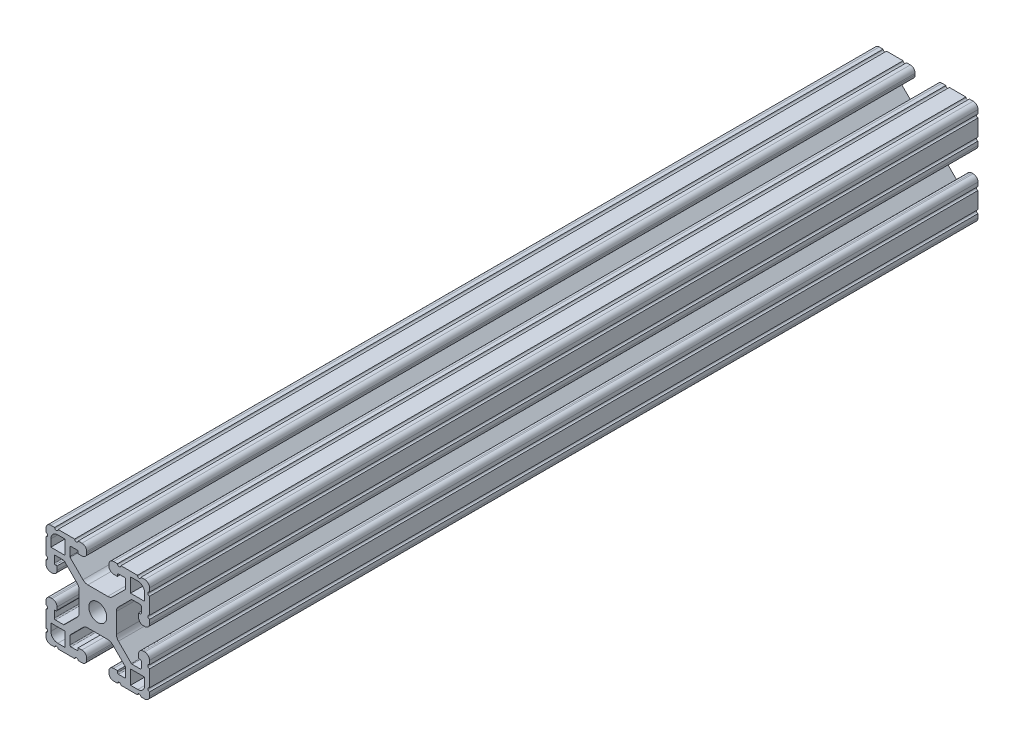
SolidWorks part; units mm, degrees
material "1023 Carbon Steel Sheet (SS)"
ref_plane "Front Plane" through (0, 0, 0) normal (0, 0, 1) x (1, 0, 0)
ref_plane "Top Plane" through (0, 0, 0) normal (0, 1, 0) x (1, 0, 0)
ref_plane "Right Plane" through (0, 0, 0) normal (1, 0, 0) x (0, 0, -1)
sketch "Sketch1" plane through (0, 0, 0) normal (0, 0, 1) x (1, 0, 0)
  line L0 (0, -19.05) -> (0, 19.05) construction
  line L1 (19.05, 0) -> (-19.05, 0) construction
  line L2 (4.064, 19.05) -> (-4.064, 19.05) construction
  line L3 (0, -6.858) -> (0, 6.858) construction
  line L4 (-4.064, 19.05) -> (-4.064, 14.986) construction
  line L5 (19.05, -10.287) -> (19.05, 10.287) construction
  line L6 (0, -3.302) -> (0, 3.302) construction
  point P4 (0, 0)
  point P8 (0, 0)
  point P11 (0, 19.05)
  point P14 (0, 0)
  point P18 (19.05, 0)
  point P21 (0, 0)
  dimension "Rail Width" = 38.1
  dimension "Rail Height" = 38.1
  dimension "T-Slot Width" = 8.128
  dimension "Thickness" = 4.064
  dimension "Opening Width" = 20.574
  dimension "Center Hole Diameter" = 6.604
  dimension "Slot Depth" = 12.192
sketch "Sketch2" plane through (0, 0, 0) normal (1, 0, 0) x (0, 0, -1)
  line L0 (-152.4, 0) -> (152.4, 0) construction
  line L1 (0, 19.05) -> (0, -19.05) construction
  line L2 (-25.4, 19.05) -> (25.4, 19.05) construction
  line L4 (3048, -19.05) -> (-3048, -19.05) construction
  point P0 (101.6, 0)
  point P3 (-101.6, 0)
  point P4 (0, 0)
  dimension "D1" = 50.8
  dimension "Rep Length" = 304.8
  dimension "D2" = 50.8
  dimension "Length Range [Min]" = 50.8
  dimension "Length Range [Max]" = 6096
sketch "Sketch3" plane through (0, 0, 0) normal (0, 0, 1) x (1, 0, 0)
  line L1 (19.05, -19.05) -> (-19.05, -19.05)
  line L2 (19.05, -19.05) -> (19.05, 19.05)
  line L3 (19.05, 19.05) -> (-19.05, 19.05)
  line L4 (-19.05, -19.05) -> (-19.05, 19.05)
  line L5 (19.05, -19.05) -> (-19.05, 19.05) construction
  line L6 (19.05, 19.05) -> (-19.05, -19.05) construction
  point P0 (0, 0)
extrude "Boss-Extrude1" add sketch "Sketch3" along normal up to vertex (152.4 mm away) and the other way up to vertex (152.4 mm away) up to point (0, 0, 152.4) other way up to point (0, 0, -152.4)
sketch "Sketch4" plane through (0, 0, 152.4) normal (0, 0, 1) x (1, 0, 0)
  line L4 (4.064, 14.986) -> (4.064, 19.05)
  line L5 (7.239, 14.986) -> (4.064, 14.986)
  line L6 (19.05, 0) -> (-19.05, 0) construction
  line L7 (4.7027, 6.858) -> (-4.7027, 6.858)
  line L8 (-4.7027, 6.858) -> (-10.287, 12.4423)
  line L37 (-19.05, 19.05) -> (-19.05, -19.05) construction
  line L38 (-19.05, -19.05) -> (19.05, -19.05) construction
  line L39 (-10.287, 12.4423) -> (-10.287, 16.002)
  line L40 (-10.287, 16.002) -> (-7.239, 16.002)
  line L41 (-7.239, 16.002) -> (-7.239, 14.986)
  line L42 (-7.239, 14.986) -> (-4.064, 14.986)
  line L43 (-4.064, 14.986) -> (-4.064, 19.05)
  line L44 (-4.064, 19.05) -> (4.064, 19.05)
  line L45 (0, 19.05) -> (0, 0) construction
  line L46 (-19.05, 19.05) -> (0, 0) construction
  line L47 (7.239, 16.002) -> (7.239, 14.986)
  line L48 (10.287, 16.002) -> (7.239, 16.002)
  line L49 (10.287, 12.4423) -> (10.287, 16.002)
  line L50 (4.7027, 6.858) -> (10.287, 12.4423)
  line L51 (-19.05, 0) -> (19.05, 0) construction
  line L52 (4.7027, -6.858) -> (10.287, -12.4423)
  line L53 (10.287, -12.4423) -> (10.287, -16.002)
  line L54 (10.287, -16.002) -> (7.239, -16.002)
  line L55 (7.239, -16.002) -> (7.239, -14.986)
  line L56 (-4.064, -19.05) -> (4.064, -19.05)
  line L57 (-4.064, -14.986) -> (-4.064, -19.05)
  line L58 (-7.239, -14.986) -> (-4.064, -14.986)
  line L59 (-7.239, -16.002) -> (-7.239, -14.986)
  line L60 (-10.287, -16.002) -> (-7.239, -16.002)
  line L61 (-10.287, -12.4423) -> (-10.287, -16.002)
  line L62 (-4.7027, -6.858) -> (-10.287, -12.4423)
  line L63 (4.7027, -6.858) -> (-4.7027, -6.858)
  line L64 (7.239, -14.986) -> (4.064, -14.986)
  line L65 (4.064, -14.986) -> (4.064, -19.05)
  line L66 (-6.858, -4.7027) -> (-12.4423, -10.287)
  line L67 (-12.4423, -10.287) -> (-16.002, -10.287)
  line L68 (-16.002, -10.287) -> (-16.002, -7.239)
  line L69 (-16.002, -7.239) -> (-14.986, -7.239)
  line L70 (-19.05, 4.064) -> (-19.05, -4.064)
  line L71 (-14.986, 4.064) -> (-19.05, 4.064)
  line L72 (-14.986, 7.239) -> (-14.986, 4.064)
  line L73 (-16.002, 7.239) -> (-14.986, 7.239)
  line L74 (-16.002, 10.287) -> (-16.002, 7.239)
  line L75 (-12.4423, 10.287) -> (-16.002, 10.287)
  line L76 (-6.858, 4.7027) -> (-12.4423, 10.287)
  line L77 (-6.858, -4.7027) -> (-6.858, 4.7027)
  line L78 (-14.986, -7.239) -> (-14.986, -4.064)
  line L79 (-14.986, -4.064) -> (-19.05, -4.064)
  line L80 (14.986, -4.064) -> (19.05, -4.064)
  line L81 (14.986, -7.239) -> (14.986, -4.064)
  line L82 (6.858, -4.7027) -> (6.858, 4.7027)
  line L83 (6.858, 4.7027) -> (12.4423, 10.287)
  line L84 (12.4423, 10.287) -> (16.002, 10.287)
  line L85 (16.002, 10.287) -> (16.002, 7.239)
  line L86 (16.002, 7.239) -> (14.986, 7.239)
  line L87 (14.986, 7.239) -> (14.986, 4.064)
  line L88 (14.986, 4.064) -> (19.05, 4.064)
  line L89 (19.05, 4.064) -> (19.05, -4.064)
  line L90 (16.002, -7.239) -> (14.986, -7.239)
  line L91 (16.002, -10.287) -> (16.002, -7.239)
  line L92 (12.4423, -10.287) -> (16.002, -10.287)
  line L93 (6.858, -4.7027) -> (12.4423, -10.287)
  line L94 (19.05, -19.05) -> (19.05, 19.05) construction
  line L95 (12.065, 17.272) -> (17.272, 17.272)
  line L96 (12.065, 17.272) -> (12.065, 12.065)
  line L97 (12.065, 12.065) -> (17.272, 12.065)
  line L98 (17.272, 17.272) -> (17.272, 12.065)
  line L99 (19.05, 19.05) -> (-19.05, 19.05) construction
  line L100 (17.272, -17.272) -> (17.272, -12.065)
  line L101 (12.065, -17.272) -> (17.272, -17.272)
  line L102 (12.065, -17.272) -> (12.065, -12.065)
  line L103 (12.065, -12.065) -> (17.272, -12.065)
  line L104 (-17.272, 17.272) -> (-17.272, 12.065)
  line L105 (-12.065, 12.065) -> (-17.272, 12.065)
  line L106 (-12.065, 17.272) -> (-12.065, 12.065)
  line L107 (-12.065, 17.272) -> (-17.272, 17.272)
  line L108 (-12.065, -12.065) -> (-17.272, -12.065)
  line L109 (-12.065, -17.272) -> (-12.065, -12.065)
  line L110 (-12.065, -17.272) -> (-17.272, -17.272)
  line L111 (-17.272, -17.272) -> (-17.272, -12.065)
  circle A5 centre (0, 0) radius 3.302
  point P21 (0, 6.858)
  point P23 (0, -6.858)
  point P38 (-6.858, 0)
  point P53 (6.858, 0)
  dimension "D1" = 20.574
  dimension "D2" = 3.048
  dimension "D3" = 3.048
  dimension "D4" = 3.048
  dimension "D5" = 1.778
  dimension "D6" = 1.778
  dimension "D7" = 1.778
extrude "Cut-Extrude1" cut sketch "Sketch4" against normal through all
sketch "Sketch5" plane through (0, 0, 152.4) normal (0, 0, 1) x (1, 0, 0)
  line L4 (-4.064, 19.05) -> (-19.05, 19.05) construction
  line L26 (-19.05, 19.05) -> (-19.05, 4.064) construction
  line L27 (-15.875, 19.05) -> (-14.605, 19.05)
  line L28 (-8.509, 19.05) -> (-7.239, 19.05)
  line L29 (-19.05, 15.875) -> (-19.05, 14.605)
  line L30 (-19.05, 8.509) -> (-19.05, 7.239)
  line L31 (8.509, 19.05) -> (7.239, 19.05)
  line L32 (15.875, 19.05) -> (14.605, 19.05)
  line L33 (19.05, 15.875) -> (19.05, 14.605)
  line L34 (19.05, 8.509) -> (19.05, 7.239)
  line L35 (19.05, -8.509) -> (19.05, -7.239)
  line L36 (19.05, -15.875) -> (19.05, -14.605)
  line L37 (15.875, -19.05) -> (14.605, -19.05)
  line L38 (8.509, -19.05) -> (7.239, -19.05)
  line L39 (-8.509, -19.05) -> (-7.239, -19.05)
  line L40 (-15.875, -19.05) -> (-14.605, -19.05)
  line L41 (-19.05, -15.875) -> (-19.05, -14.605)
  line L42 (-19.05, -8.509) -> (-19.05, -7.239)
  line L43 (19.05, 19.05) -> (4.064, 19.05) construction
  line L44 (19.05, 4.064) -> (19.05, 19.05) construction
  line L48 (-14.986, 4.064) -> (-19.05, 4.064) construction
  line L49 (-4.064, 14.986) -> (-4.064, 19.05) construction
  arc A8 (-15.875, 19.05) -> (-14.605, 19.05) centre (-15.24, 19.05) ccw
  arc A9 (-8.509, 19.05) -> (-7.239, 19.05) centre (-7.874, 19.05) ccw
  arc A10 (-19.05, 14.605) -> (-19.05, 15.875) centre (-19.05, 15.24) ccw
  arc A11 (-19.05, 7.239) -> (-19.05, 8.509) centre (-19.05, 7.874) ccw
  arc A12 (7.239, 19.05) -> (8.509, 19.05) centre (7.874, 19.05) ccw
  arc A13 (14.605, 19.05) -> (15.875, 19.05) centre (15.24, 19.05) ccw
  arc A14 (19.05, 15.875) -> (19.05, 14.605) centre (19.05, 15.24) ccw
  arc A15 (19.05, 8.509) -> (19.05, 7.239) centre (19.05, 7.874) ccw
  arc A16 (19.05, -7.239) -> (19.05, -8.509) centre (19.05, -7.874) ccw
  arc A17 (19.05, -14.605) -> (19.05, -15.875) centre (19.05, -15.24) ccw
  arc A18 (15.875, -19.05) -> (14.605, -19.05) centre (15.24, -19.05) ccw
  arc A19 (8.509, -19.05) -> (7.239, -19.05) centre (7.874, -19.05) ccw
  arc A20 (-7.239, -19.05) -> (-8.509, -19.05) centre (-7.874, -19.05) ccw
  arc A21 (-14.605, -19.05) -> (-15.875, -19.05) centre (-15.24, -19.05) ccw
  arc A22 (-19.05, -15.875) -> (-19.05, -14.605) centre (-19.05, -15.24) ccw
  arc A23 (-19.05, -8.509) -> (-19.05, -7.239) centre (-19.05, -7.874) ccw
  dimension "D2" = 0.635
  dimension "D4" = 3.81
  dimension "D5" = 3.81
  dimension "D1" = 3.81
  dimension "D3" = 3.81
  dimension "D7" = 4
extrude "Cut-Extrude2" cut sketch "Sketch5" against normal through all
fillet "Fillet1" radius 2.54 12 edges at (-6.858, 4.7027, 0) (-6.858, -4.7027, 0) (4.7027, -6.858, 0) (-4.7027, -6.858, 0) (6.858, -4.7027, 0) (6.858, 4.7027, 0) (4.7027, 6.858, 0) (-4.7027, 6.858, 0) (-17.272, 17.272, 0) (17.272, 17.272, 0) (17.272, -17.272, 0) (-17.272, -17.272, 0)
fillet "Fillet2" radius 1.778 20 edges at (19.05, -19.05, 0) (19.05, 19.05, 0) (-19.05, -19.05, 0) (-19.05, 19.05, 0) (-14.986, 4.064, 0) (-19.05, 4.064, 0) (-19.05, -4.064, 0) (-14.986, -4.064, 0) (-4.064, -19.05, 0) (-4.064, -14.986, 0) (4.064, -14.986, 0) (4.064, -19.05, 0) (19.05, -4.064, 0) (14.986, -4.064, 0) (19.05, 4.064, 0) (14.986, 4.064, 0) (4.064, 14.986, 0) (4.064, 19.05, 0) (-4.064, 19.05, 0) (-4.064, 14.986, 0)
fillet "Fillet3" radius 0.3969 24 edges at (-14.986, -7.239, 0) (-16.002, -10.287, 0) (-12.4423, -10.287, 0) (-12.4423, 10.287, 0) (-16.002, 7.239, 0) (-16.002, 10.287, 0) (-10.287, 12.4423, 0) (-7.239, 16.002, 0) (-10.287, 16.002, 0) (10.287, 16.002, 0) (7.239, 16.002, 0) (10.287, 12.4423, 0) (16.002, 10.287, 0) (12.4423, 10.287, 0) (16.002, 7.239, 0) (16.002, -7.239, 0) (16.002, -10.287, 0) (12.4423, -10.287, 0) (10.287, -12.4423, 0) (10.287, -16.002, 0) (7.239, -16.002, 0) (-7.239, -16.002, 0) (-10.287, -12.4423, 0) (-10.287, -16.002, 0)
sketch "Sketch6" plane through (0, 0, 152.4) normal (0, 0, 1) x (1, 0, 0)
  line L1 (-21.5207, 20.8878) -> (21.5207, 20.8878)
  line L2 (-21.5207, 20.8878) -> (-21.5207, -20.8878)
  line L3 (-21.5207, -20.8878) -> (21.5207, -20.8878)
  line L4 (21.5207, 20.8878) -> (21.5207, -20.8878)
  line L5 (-21.5207, 20.8878) -> (21.5207, -20.8878) construction
  line L6 (-21.5207, -20.8878) -> (21.5207, 20.8878) construction
  point P0 (0, 0)
equation "\"D4@Sketch5\"=\"D3@Sketch5\""
equation "\"D5@Sketch5\"=\"D4@Sketch5\""
equation "\"D1@Sketch4\"=\"Opening Width@Sketch1\""
